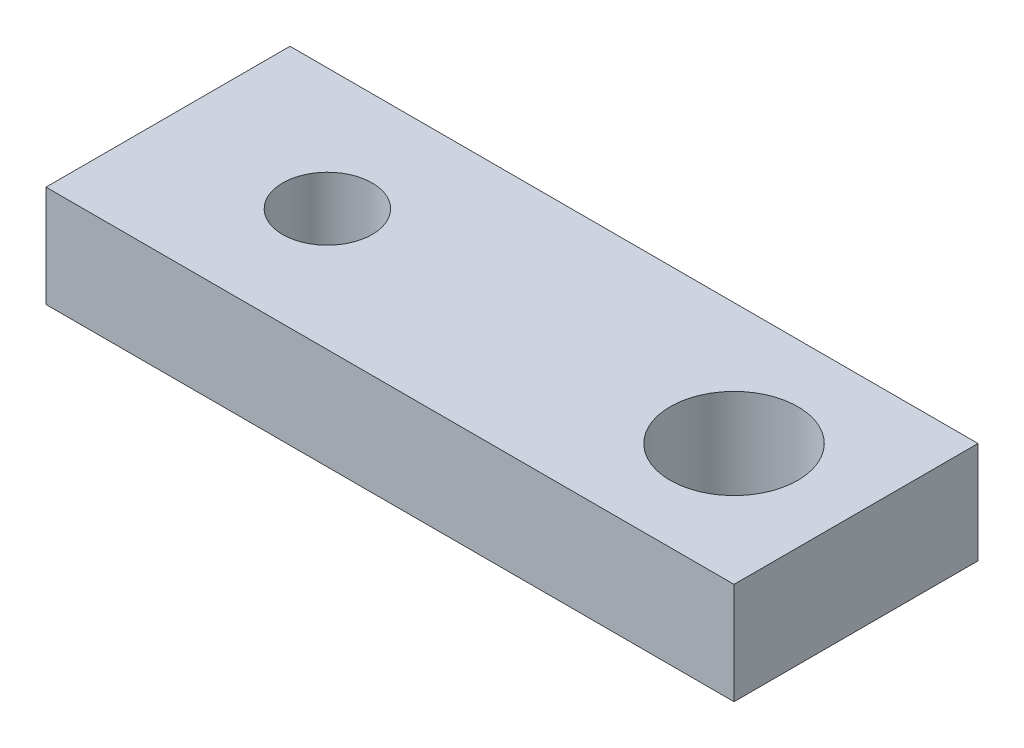
SolidWorks part; units mm, degrees
ref_plane "Front Plane" through (0, 0, 0) normal (0, 0, 1) x (1, 0, 0)
ref_plane "Top Plane" through (0, 0, 0) normal (0, 1, 0) x (1, 0, 0)
ref_plane "Right Plane" through (0, 0, 0) normal (1, 0, 0) x (0, 0, -1)
sketch "Sketch1" plane through (0, 0, 0) normal (0, 1, 0) x (1, 0, 0)
  line L0 (12.7, 1.9939) -> (12.7, 3.81) construction
  line L1 (-4.9784, 3.81) -> (16.51, 3.81)
  line L2 (-4.9784, 3.81) -> (-4.9784, -3.81)
  line L3 (-4.9784, -3.81) -> (16.51, -3.81)
  line L4 (16.51, 3.81) -> (16.51, -3.81)
  line L5 (14.6939, 0) -> (16.51, 0) construction
  circle A0 centre (0, 0) radius 1.397
  circle A1 centre (12.7, 0) radius 1.9939
  point P9 (-4.9784, 0)
  dimension "D1" = 2.794
  dimension "D2" = 3.9878
  dimension "D3" = 12.7
  dimension "D4" = 7.62
  dimension "D5" = 4.9784
extrude "Boss-Extrude3" add sketch "Sketch1" along normal blind 3.175
